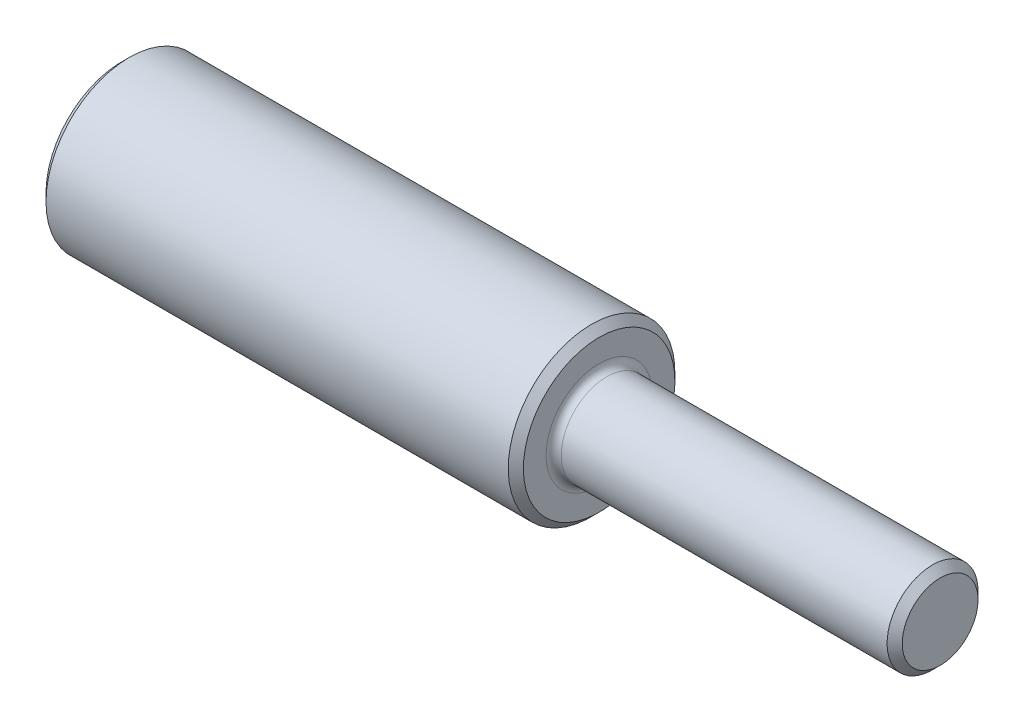
SolidWorks part; units mm, degrees
material "1.0116 (S235J2G3)"
ref_plane "Front Plane" through (0, 0, 0) normal (0, 0, 1) x (1, 0, 0)
ref_plane "Top Plane" through (0, 0, 0) normal (0, 1, 0) x (1, 0, 0)
ref_plane "Right Plane" through (0, 0, 0) normal (1, 0, 0) x (0, 0, -1)
sketch "Sketch1" plane through (0, 0, 0) normal (0, 0, 1) x (1, 0, 0)
  line L0 (113.8338, 0) -> (-74.9098, 0) construction
  line L1 (0, 0) -> (0, 11)
  line L2 (0, 11) -> (63, 11)
  line L3 (63, 11) -> (63, 7)
  line L4 (64, 6) -> (108, 6)
  line L5 (108, 6) -> (108, 0)
  line L6 (0, 0) -> (108, 0)
  arc A0 (63, 7) -> (64, 6) centre (64, 7) ccw
  point P12 (63, 6)
  dimension "D5" = 1
  dimension "D1" = 11
  dimension "D2" = 45
  dimension "D3" = 6
  dimension "D4" = 108
revolve "Revolve1" add sketch "Sketch1" angle 360 about L0
sketch "Sketch2" plane through (0, 0, 0) normal (-1, 0, 0) x (0, 0, 1)
  line L0 (-9.3, -2.5) -> (-6.5383, -2.5)
  line L1 (-9.3, -2.5) -> (-9.3, 2.5)
  line L2 (-9.3, 2.5) -> (-6.5383, 2.5)
  line L3 (-9.3, -2.5) -> (-4.9647, 2.2123) construction
  line L4 (-9.3, 2.5) -> (-4.9647, -2.2123) construction
  arc A0 (-6.5383, -2.5) -> (-6.5383, 2.5) centre (0, 0) ccw
  point P2 (-7, 0)
  dimension "D1" = 14
  dimension "D2" = 5
  dimension "D3" = 9.3
extrude "Cut-Extrude1" cut sketch "Sketch2" against normal blind 35
chamfer "Chamfer2" distance 1 angle 45 4 edges at (0, 0, 7) (108, 6, 0) (63, 11, 0) (0, 11, 0)
